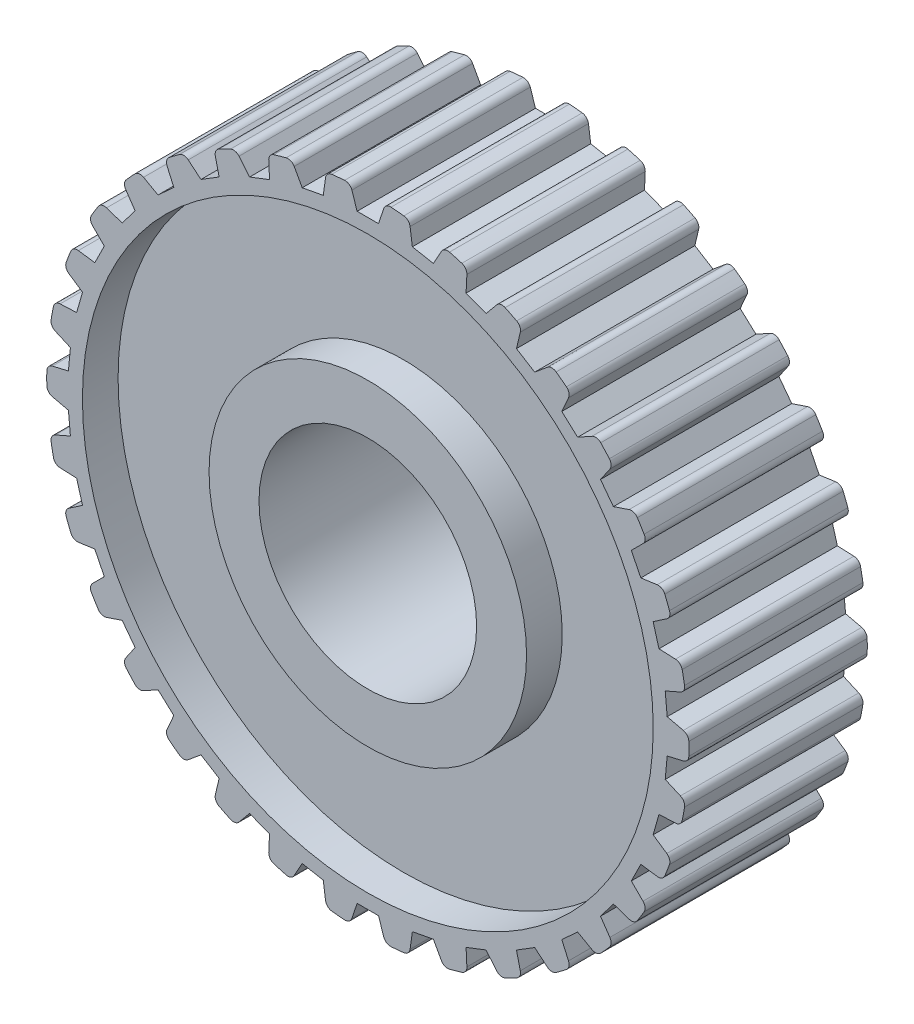
SolidWorks part; units mm, degrees
ref_plane "Front Plane" through (0, 0, 0) normal (0, 0, 1) x (1, 0, 0)
ref_plane "Top Plane" through (0, 0, 0) normal (0, 1, 0) x (1, 0, 0)
ref_plane "Right Plane" through (0, 0, 0) normal (1, 0, 0) x (0, 0, -1)
sketch "Sketch1" plane through (0, 0, 0) normal (0, 0, 1) x (1, 0, 0)
  line L0 (-3.6584, 0) -> (7.3024, 0) construction
  line L1 (0, 2.8671) -> (0, -5.0294) construction
  circle A3 centre (0, 0) radius 45
  circle A4 centre (0, 0) radius 40
  circle A5 centre (0, 0) radius 22.25
  circle A6 centre (0, 0) radius 15.25
extrude "Boss-Extrude1" add sketch "Sketch1" along normal blind 25 contours A3 A4 | A5 A6
ref_plane "Plane1" through (0, 0, 12.5) normal (0, 0, 1) x (1, 0, 0)
sketch "Sketch2" plane through (0, 0, 12.5) normal (0, 0, 1) x (1, 0, 0)
  circle A0 centre (0, 0) radius 40
  circle A1 centre (0, 0) radius 22.25
extrude "Boss-Extrude2" add sketch "Sketch2" along normal blind 7.5 and the other way blind 7.5
sketch "Sketch4" plane through (0, 0, 25) normal (0, 0, 1) x (1, 0, 0)
  line L0 (-2.5, 1.5) -> (2.5, 1.5)
  line L1 (0, -1.5) -> (1.5, -1.5)
  line L2 (0, -1.5) -> (-1.5, -1.5)
  line L8 (-2.5, 45) -> (2.5, 45)
  line L9 (0, 42) -> (1.5, 42)
  line L10 (0, 42) -> (-1.5, 42)
  line L11 (-2.5, 45) -> (-1.5, 42)
  line L12 (1.5, 42) -> (2.5, 45)
  line L13 (-2.5, 1.5) -> (-1.5, -1.5)
  line L14 (1.5, -1.5) -> (2.5, 1.5)
  dimension "D1" = 5
  dimension "D2" = 5
extrude "Cut-Extrude2" cut sketch "Sketch4" against normal through all contours L8 L12 L9 L10 L11
fillet "Fillet1" radius 1 2 edges at (2.4773, 44.9318, 12.5) (-2.4773, 44.9318, 12.5)
pattern_circular "CirPattern1" count 34 over 360 about axis through (0, 0, 0) along (0, 0, 1) of "Cut-Extrude2", "Fillet1"
